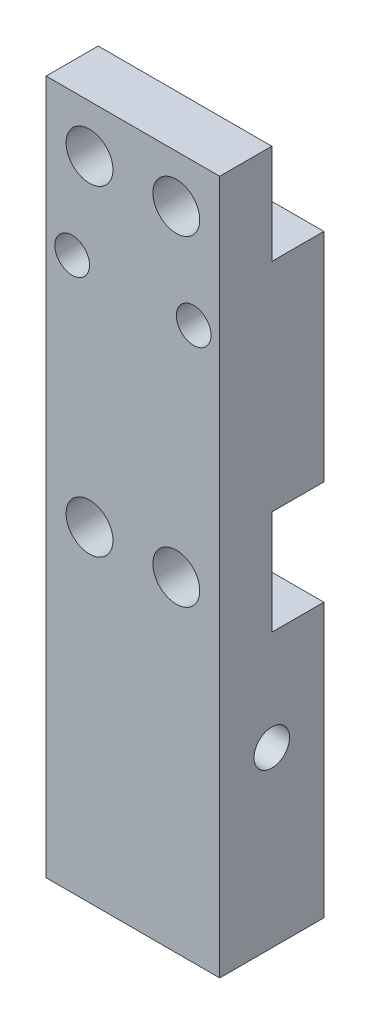
SolidWorks part; units mm, degrees
material "Ceramic Porcelain"
ref_plane "Front Plane" through (0, 0, 0) normal (0, 0, 1) x (1, 0, 0)
ref_plane "Top Plane" through (0, 0, 0) normal (0, 1, 0) x (1, 0, 0)
ref_plane "Right Plane" through (0, 0, 0) normal (1, 0, 0) x (0, 0, -1)
sketch "Sketch1" plane through (0, 0, 0) normal (0, 1, 0) x (1, 0, 0)
  line L1 (-5, 3) -> (5, 3)
  line L2 (-5, 3) -> (-5, -3)
  line L3 (-5, -3) -> (5, -3)
  line L4 (5, 3) -> (5, -3)
  point P4 (0, 3)
  point P6 (5, 0)
  dimension "D1" = 10
  dimension "D2" = 6
extrude "Boss-Extrude1" add sketch "Sketch1" along normal blind 40
hole_wizard "M2.5 Tapped Hole1" positions "Sketch4" profile "Sketch5" tap size "M2.5" standard "ISO"
sketch "Sketch4" plane through (0, 0, 0) normal (0, -1, 0) x (-1, 0, 0)
  line L0 (-5, 3) -> (5, 3) construction
  line L1 (-5, -3) -> (-5, 3) construction
  line L2 (-5, 3) -> (5, 3)
  line L3 (-5, -3) -> (-5, 3)
  line L4 (5, 3) -> (5, -3) construction
  point P0 (2.5, 0)
  point P2 (-2.5, 0)
  point P9 (-5, 0)
  dimension "D1" = 2.5
  dimension "D2" = 2.5
cosmetic thread "Hole Thread1" parameters "D1"=5, "D2"=2.5
cosmetic thread "Hole Thread2" parameters "D1"=5, "D2"=2.5
sketch "Sketch5" plane through (-2.5, 0, 0) normal (1, 0, 0) x (0, 0, -1)
  line L0 (0, 0) -> (0, 10.6159)
  line L1 (0, 10.6159) -> (1.025, 10)
  line L2 (1.025, 10) -> (1.025, 0)
  line L5 (1.025, 0) -> (0, 0)
  line L10 (0, 10.6159) -> (-1.025, 10) construction
  line L11 (0, -6.35) -> (0, 107.95) construction
  dimension "Tap Drill Dia." = 2.05
  dimension "Tap Drill Depth" = 10
  dimension "Drill Angle" = 118
hole_wizard "M2.5 Clearance Hole1" positions "Sketch6" profile "Sketch7" hole size "M2.5" standard "ISO" end condition through all
sketch "Sketch6" plane through (0, 0, -3) normal (0, 0, -1) x (-1, 0, 0)
  line L0 (5, 40) -> (5, 0) construction
  line L1 (-5, 40) -> (-5, 0) construction
  line L2 (-5, 40) -> (5, 40) construction
  line L3 (5, 40) -> (5, 0)
  line L4 (-5, 40) -> (-5, 0)
  line L5 (-5, 40) -> (5, 40)
  line L11 (-5, 17) -> (5, 17)
  line L13 (-5, 35.5) -> (5.4272, 35.5)
  point P0 (-2.5, 37.25)
  point P2 (2.5, 37.25)
  point P4 (-2.5, 18.75)
  point P6 (2.5, 18.75)
  dimension "D1" = 2.5
  dimension "D2" = 2.5
  dimension "D3" = 4.5
  dimension "D4" = 23
  dimension "D5" = 1.75
  dimension "D6" = 1.75
sketch "Sketch7" plane through (2.5, 37.25, -3) normal (1, 0, 0) x (0, 1, 0)
  line L0 (0, 0) -> (0, 6)
  line L1 (0, 6) -> (1.35, 6)
  line L2 (1.35, 6) -> (1.35, 0)
  line L5 (1.35, 0) -> (0, 0)
  line L11 (0, -6.35) -> (0, 107.95) construction
  dimension "Thru Hole Dia." = 2.7
  dimension "Thru Hole Depth" = 6
hole_wizard "Ø2.0 (2) Diameter Hole2" positions "Sketch8" profile "Sketch9" hole size "Ø2.0" standard "ISO" end condition through all
sketch "Sketch8" plane through (0, 0, -3) normal (0, 0, -1) x (-1, 0, 0)
  line L0 (-6.3768, 31.81) -> (16.7892, 31.81) construction
  line L1 (5, 40) -> (5, 0) construction
  point P0 (3.5, 31.81)
  dimension "D1" = 1.5
sketch "Sketch9" plane through (-3.5, 31.81, -3) normal (1, 0, 0) x (0, 1, 0)
  line L0 (0, 0) -> (0, 6)
  line L1 (0, 6) -> (1, 6)
  line L2 (1, 6) -> (1, 0)
  line L5 (1, 0) -> (0, 0)
  line L11 (0, -6.35) -> (0, 107.95) construction
  dimension "Thru Hole Dia." = 2
  dimension "Thru Hole Depth" = 6
mirror "Mirror1" about plane through (0, 0, 0) normal (1, 0, 0) of "Ø2.0 (2) Diameter Hole2"
hole_wizard "M2.5 Tapped Hole2" positions "Sketch10" profile "Sketch11" tap size "M2.5" standard "ISO" end condition through all
sketch "Sketch10" plane through (5, 0, 0) normal (1, 0, 0) x (0, 0, -1)
  line L0 (-3, 0) -> (3, 0) construction
  line L1 (-3, 0) -> (3, 0)
  point P0 (0, 10)
  point P5 (0, 0)
  dimension "D1" = 10
sketch "Sketch11" plane through (5, 10, 0) normal (0, 1, 0) x (0, 0, -1)
  line L0 (0, 0) -> (0, 10)
  line L1 (0, 10) -> (1.025, 10)
  line L2 (1.025, 10) -> (1.025, 0)
  line L5 (1.025, 0) -> (0, 0)
  line L11 (0, -6.35) -> (0, 107.95) construction
  dimension "Thru Tap Drill Dia." = 2.05
  dimension "Thru Tap Drill Depth" = 10
cosmetic thread "Hole Thread3" parameters "D2"=2.5
sketch "Sketch13" plane through (0, 0, -3) normal (0, 0, -1) x (-1, 0, 0)
  line L0 (-5, 40) -> (-5, 0) construction
  line L1 (-5, 21.75) -> (5, 21.75)
  line L2 (-5, 21.75) -> (-5, 15.75)
  line L3 (-5, 15.75) -> (5, 15.75)
  line L4 (5, 21.75) -> (5, 15.75)
  line L5 (5, 40) -> (5, 0) construction
  line L7 (-5, 40) -> (5, 40)
  line L8 (-5, 40) -> (-5, 34.25)
  line L9 (-5, 34.25) -> (5, 34.25)
  line L10 (5, 40) -> (5, 34.25)
  circle A0 centre (-2.5, 37.25) radius 1.35 construction
  circle A1 centre (-2.5, 18.75) radius 1.35 construction
  dimension "D1" = 3
  dimension "D2" = 3
  dimension "D3" = 6
extrude "Cut-Extrude2" cut sketch "Sketch13" against normal blind 3
